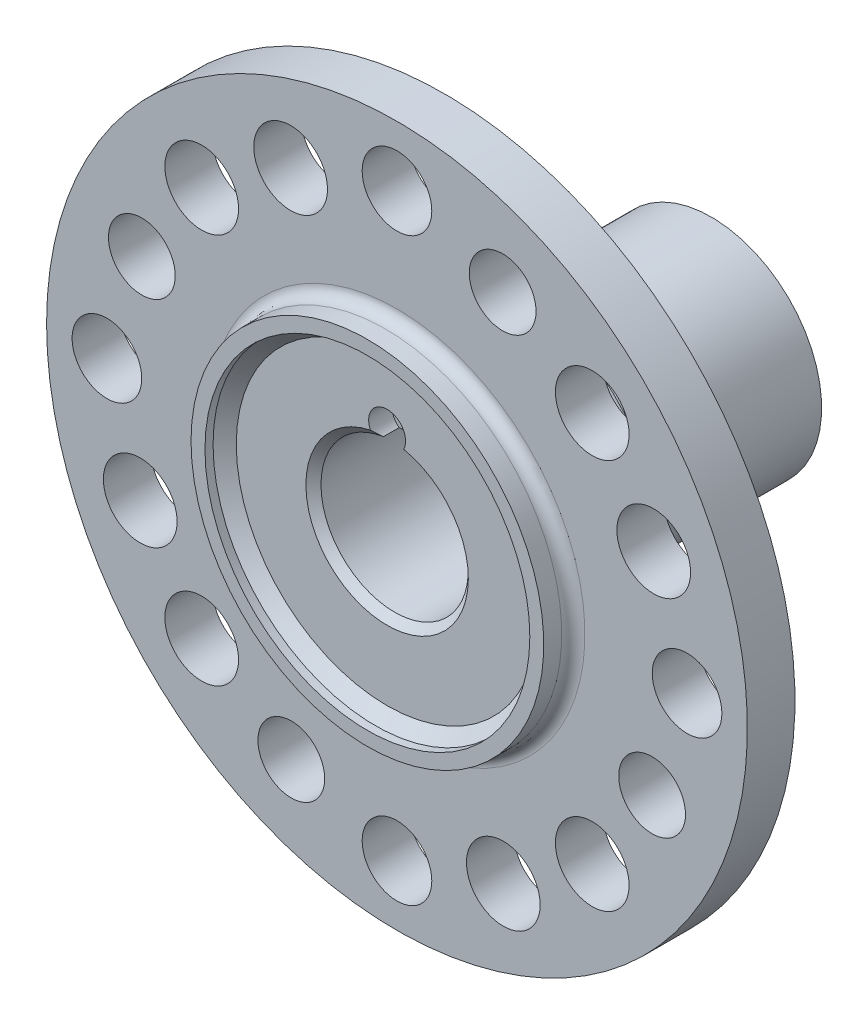
SolidWorks part; units mm, degrees
material "AISI 4130 Steel, normalized at 870C"
ref_plane "Front Plane" through (0, 0, 0) normal (0, 0, 1) x (1, 0, 0)
ref_plane "Top Plane" through (0, 0, 0) normal (0, 1, 0) x (1, 0, 0)
ref_plane "Right Plane" through (0, 0, 0) normal (1, 0, 0) x (0, 0, -1)
sketch "Sketch1" plane through (0, 0, 0) normal (1, 0, 0) x (0, 0, -1)
  line L0 (0.5, 19) -> (38, 19)
  line L1 (38, 19) -> (38, 18)
  line L2 (38, 18) -> (34.1, 14.1)
  line L3 (34.1, 14.1) -> (18.3, 14.1)
  line L4 (18.3, 14.1) -> (16.9, 12.7)
  line L5 (16.9, 12.7) -> (-16.6, 12.7)
  line L6 (-16.6, 12.7) -> (-17.9, 14)
  line L7 (-17.9, 14) -> (-17.9, 20.7)
  line L8 (0, 19.5) -> (0, 25.25)
  line L9 (0, 25.25) -> (-3.6, 28.85)
  line L10 (-3.6, 28.85) -> (-3.6, 35.7)
  line L11 (-3.6, 35.7) -> (-5.45, 35.7)
  line L12 (-7.45, 37.7) -> (-7.45, 38.8)
  line L13 (-7.45, 38.8) -> (-7.5, 38.8)
  line L14 (-8, 39.3) -> (-8, 60.4)
  line L15 (-8, 60.4) -> (-16.2, 60.4)
  line L16 (-16.2, 60.4) -> (-16.2, 32.4)
  line L17 (-18.2, 30.4) -> (-21.3, 30.4)
  line L18 (-21.3, 30.4) -> (-21.3, 29.9)
  line L19 (-23.3, 27.9) -> (-27.5, 27.9)
  line L20 (-27.5, 27.9) -> (-27.5, 25.3)
  line L21 (-27.5, 25.3) -> (-22.3, 25.3)
  line L22 (-20.3, 23.3) -> (-20.3, 21.7)
  line L23 (-20.3, 21.7) -> (-18.9, 21.7)
  line L25 (0, 0) -> (-74.9273, 0) construction
  arc A0 (0.5, 19) -> (0, 19.5) centre (0.5, 19.5) cw
  arc A1 (-5.45, 35.7) -> (-7.45, 37.7) centre (-5.45, 37.7) cw
  arc A2 (-7.5, 38.8) -> (-8, 39.3) centre (-7.5, 39.3) cw
  arc A3 (-22.3, 25.3) -> (-20.3, 23.3) centre (-22.3, 23.3) cw
  arc A4 (-21.3, 29.9) -> (-23.3, 27.9) centre (-23.3, 29.9) cw
  arc A5 (-16.2, 32.4) -> (-18.2, 30.4) centre (-18.2, 32.4) cw
  arc A6 (-18.9, 21.7) -> (-17.9, 20.7) centre (-18.9, 20.7) cw
  point P30 (0, 19)
  point P39 (-21.3, 27.9)
  dimension "D25" = 0.5
  dimension "D26" = 2
  dimension "D27" = 0.5
  dimension "D28" = 2
  dimension "D29" = 1
  dimension "D1" = 120.8
  dimension "D2" = 38
  dimension "D3" = 1
  dimension "D4" = 28.2
  dimension "D5" = 45
  dimension "D6" = 15.8
  dimension "D7" = 25.4
  dimension "D8" = 38
  dimension "D9" = 50.5
  dimension "D10" = 3.6
  dimension "D11" = 71.4
  dimension "D12" = 0.55
  dimension "D13" = 77.6
  dimension "D14" = 4.4
  dimension "D15" = 8.2
  dimension "D16" = 55.8
  dimension "D17" = 60.8
  dimension "D18" = 65.5
  dimension "D19" = 6.2
  dimension "D20" = 28
  dimension "D21" = 2.6
  dimension "D22" = 9.6
  dimension "D23" = 7.2
  dimension "D24" = 43.4
revolve "Revolve1" add sketch "Sketch1" angle 360 about L25
sketch "Sketch11" plane through (0, 0, 0) normal (0, 0, 1) x (1, 0, 0)
  circle A0 centre (0, 50) radius 6
  circle A1 centre (50, 0) radius 6
  circle A2 centre (0, -50) radius 6
  circle A3 centre (-50, 0) radius 6
  point P12 (0, 0)
  dimension "D1" = 12
  dimension "D3" = 4
  dimension "D2" = 50
extrude "Cut-Extrude4" cut sketch "Sketch11" along normal through all
sketch "Sketch2" plane through (0, 0, 0) normal (1, 0, 0) x (0, 0, -1)
  line L0 (-23.9376, 50) -> (16.7376, 50) construction
  line L1 (-46.2, 44.2) -> (-8, 44.2) construction
  line L2 (-8, -60.4) -> (-8, 60.4) construction
  line L3 (-8, 58.75) -> (-8, 55.8)
  line L4 (-46.2, 55.8) -> (-8, 55.8)
  line L5 (-8, 44.2) -> (-8, 41.25) construction
  line L6 (-46.2, 55.8) -> (-46.2, 50)
  line L7 (-8, 58.75) -> (-5.5, 58.75)
  line L8 (-5.5, 58.75) -> (-3.6, 56.9)
  line L9 (-3.6, 56.9) -> (-3.6, 50)
  line L10 (-5.5, 41.25) -> (-3.6, 43.1) construction
  line L11 (-8, 41.25) -> (-5.5, 41.25) construction
  line L13 (-46.2, 50) -> (-3.6, 50)
  line L14 (-3.6, 50) -> (-3.6, 43.1) construction
  line L15 (-46.2, 50) -> (-46.2, 44.2) construction
  point P15 (-3.6, 50)
  dimension "D1" = 50
  dimension "D3" = 17.5
  dimension "D4" = 11.6
  dimension "D6" = 13.8
  dimension "D7" = 2.5
revolve "Revolve3" [suppressed] add sketch "Sketch2" angle 360 about L0
pattern_circular "CirPattern2" [suppressed] count 4 over 360
sketch "Sketch4" plane through (0, 0, 0) normal (1, 0, 0) x (0, 0, -1)
  line L0 (-7, 60.4832) -> (-7, 39.9952)
  line L1 (-7, 39.9952) -> (12.4061, 39.9952)
  line L2 (12.4061, 39.9952) -> (12.4061, 60.4832)
  line L3 (12.4061, 60.4832) -> (-7, 60.4832)
  line L4 (-8, -60.4) -> (-8, 60.4) construction
  line L5 (0, 0) -> (50.228, 0) construction
  dimension "D1" = 1
revolve "LatheTrimBolts" [suppressed] cut sketch "Sketch4" angle 360 about L5
sketch "Sketch5" plane through (0, 0, 0) normal (1, 0, 0) x (0, 0, -1)
  line L0 (-16.2, 60.4) -> (-16.2, -60.4) construction
  line L1 (-28.2, 70.4741) -> (-61.4144, 70.4741)
  line L2 (-28.2, 70.4741) -> (-28.2, 34.279)
  line L3 (-28.2, 34.279) -> (-61.4144, 34.279)
  line L4 (-61.4144, 70.4741) -> (-61.4144, 34.279)
  line L5 (-1.1501, 0) -> (-66.0136, 0) construction
  dimension "D1" = 12
revolve "LatheTrimBolts2" [suppressed] cut sketch "Sketch5" angle 360 about L5
sketch "Sketch7" plane through (0, 0, 0) normal (1, 0, 0) x (0, 0, -1)
  line L0 (-19.9, 28) -> (-17.9, 26)
  line L1 (-17.9, 26) -> (-17.9, 0)
  line L2 (-21.3, 28) -> (-21.3, 34.5114)
  line L3 (-17.9, 0) -> (-30.1633, 0)
  line L4 (-30.1633, 0) -> (-30.1633, 25.3)
  line L5 (0, 0) -> (-41.9984, 0) construction
  line L6 (-17.9, 20.7) -> (-17.9, -20.7) construction
  line L7 (-19.9, 28) -> (-21.3, 28)
  line L8 (-30.1633, 28) -> (-30.1633, 25.3)
  line L9 (-21.3, 34.5114) -> (-30.1633, 34.5114)
  line L10 (-30.1633, 34.5114) -> (-30.1633, 28)
  line L11 (-21.3, 29.9) -> (-21.3, -29.9) construction
  point P13 (-17.9, 28)
  dimension "D2" = 0
  dimension "D4" = 56
revolve "LatheCutPocket" cut sketch "Sketch7" angle 360 about L5
sketch "Sketch8" plane through (0, 0, 8) normal (0, 0, 1) x (1, 0, 0)
  line L0 (0, 0) -> (0, 65.1382) construction
  line L1 (0, 0) -> (18.2157, 43.9767) construction
  circle A0 centre (18.2157, 43.9767) radius 6.75
  circle A1 centre (43.9767, -18.2157) radius 6.75
  circle A2 centre (-18.2157, -43.9767) radius 6.75
  circle A3 centre (-43.9767, 18.2157) radius 6.75
  point P14 (0, 0)
  dimension "D3" = 13.5
  dimension "D1" = 22.5
  dimension "D2" = 47.6
  dimension "D4" = 4
hole_wizard "1/2-20 Tapped Hole1" positions "Sketch13" profile "Sketch12" tap size "1/2-20" standard "ANSI Inch" end condition through all
sketch "Sketch13" plane through (0, 0, 16.2) normal (0, 0, 1) x (1, 0, 0)
  point P0 (18.2157, 43.9767)
  point P2 (43.9767, -18.2157)
  point P4 (-18.2157, -43.9767)
  point P6 (-43.9767, 18.2157)
sketch "Sketch12" plane through (18.2157, 43.9767, 16.2) normal (1, 0, 0) x (0, -1, 0)
  line L0 (0, 0) -> (0, 54.2)
  line L1 (0, 54.2) -> (5.7544, 54.2)
  line L2 (5.7544, 54.2) -> (5.7544, 0)
  line L5 (5.7544, 0) -> (0, 0)
  line L11 (0, -6.35) -> (0, 107.95) construction
  dimension "Thru Tap Drill Dia." = 11.5087
  dimension "Thru Tap Drill Depth" = 54.2
cosmetic thread "Hole Thread1" parameters "D2"=12.7
cosmetic thread "Hole Thread2" parameters "D2"=12.7
cosmetic thread "Hole Thread3" parameters "D2"=12.7
cosmetic thread "Hole Thread4" parameters "D2"=12.7
sketch "Sketch14" plane through (0, 0, 0) normal (0, 0, 1) x (1, 0, 0)
  line L0 (0, 0) -> (0, 70.9536) construction
  line L1 (0, 0) -> (33.6583, 33.6583) construction
  line L2 (0, 0) -> (44.2541, 18.3307) construction
  line L3 (0, 0) -> (18.2157, 43.9767) construction
  circle A0 centre (33.6583, 33.6583) radius 6.35
  circle A1 centre (44.2541, 18.3307) radius 6.35
  circle A2 centre (33.6583, -33.6583) radius 6.35
  circle A3 centre (18.3307, -44.2541) radius 6.35
  circle A4 centre (-33.6583, -33.6583) radius 6.35
  circle A5 centre (-44.2541, -18.3307) radius 6.35
  circle A6 centre (-33.6583, 33.6583) radius 6.35
  circle A7 centre (-18.3307, 44.2541) radius 6.35
  point P22 (0, 0)
  dimension "D3" = 12.7
  dimension "D1" = 45
  dimension "D2" = 22.5
  dimension "D4" = 4
extrude "Cut-Extrude5" cut sketch "Sketch14" along normal through all
sketch "Sketch15" plane through (0, 0, 17.9) normal (0, 0, 1) x (1, 0, 0)
  circle A0 centre (0, 15.075) radius 3.175
  dimension "D1" = 6.35
  dimension "D2" = 15.075
extrude "Cut-Extrude6" cut sketch "Sketch15" against normal blind 4
